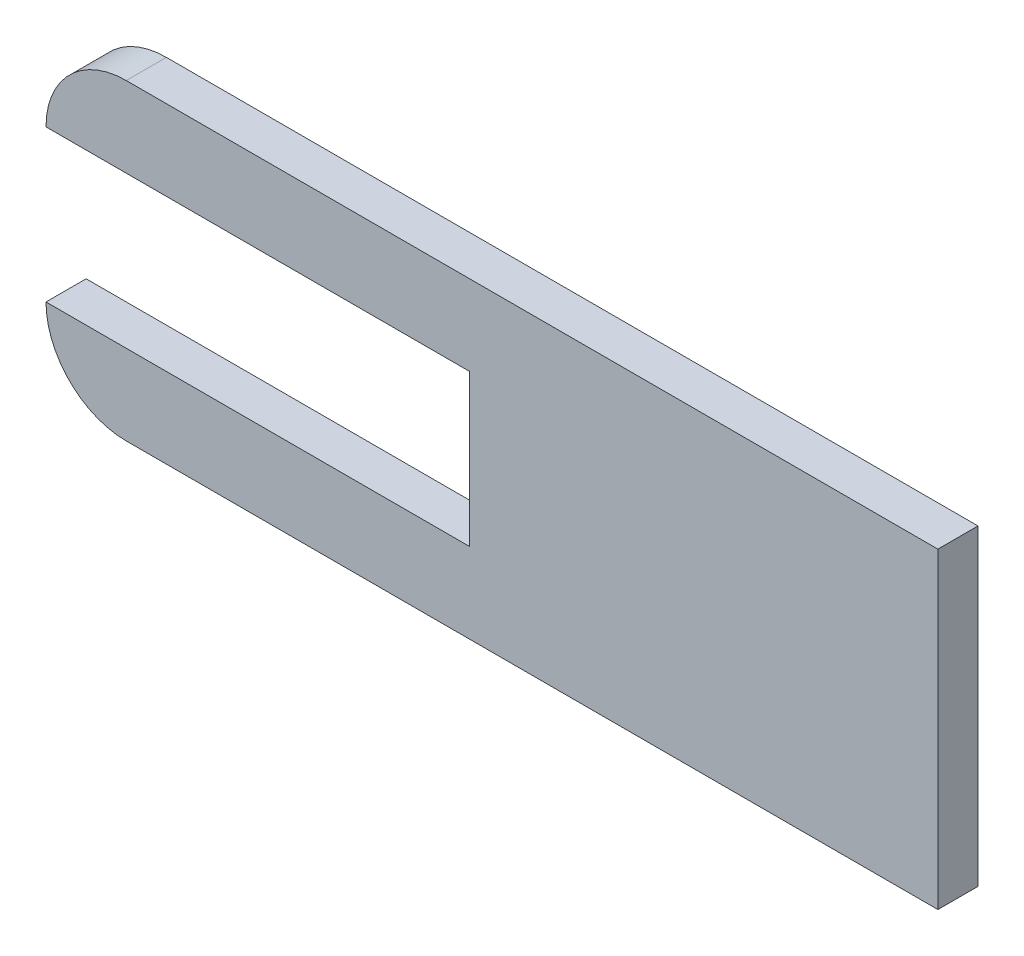
SolidWorks part; units mm, degrees
ref_plane "Front Plane" through (0, 0, 0) normal (0, 0, 1) x (1, 0, 0)
ref_plane "Top Plane" through (0, 0, 0) normal (0, 1, 0) x (1, 0, 0)
ref_plane "Right Plane" through (0, 0, 0) normal (1, 0, 0) x (0, 0, -1)
sketch "Sketch1" plane through (0, 0, 0) normal (0, 0, 1) x (1, 0, 0)
  line L1 (0, 0) -> (254, 0)
  line L2 (0, 0) -> (0, 88.9)
  line L3 (0, 88.9) -> (254, 88.9)
  line L4 (254, 0) -> (254, 88.9)
  dimension "D1" = 88.9
  dimension "D2" = 254
extrude "Boss-Extrude1" add sketch "Sketch1" along normal blind 11.43
fillet "Fillet1" radius 22.86 1 edges at (0, 88.9, 5.715)
fillet "Fillet2" radius 22.86 1 edges at (0, 0, 5.715)
sketch "Sketch2" plane through (0, 0, 0) normal (-1, 0, 0) x (0, 0, 1)
  line L1 (0, 22.86) -> (11.43, 22.86)
  line L2 (0, 22.86) -> (0, 66.04)
  line L3 (0, 66.04) -> (11.43, 66.04)
  line L4 (11.43, 22.86) -> (11.43, 66.04)
extrude "Cut-Extrude1" cut sketch "Sketch2" against normal blind 120.65
